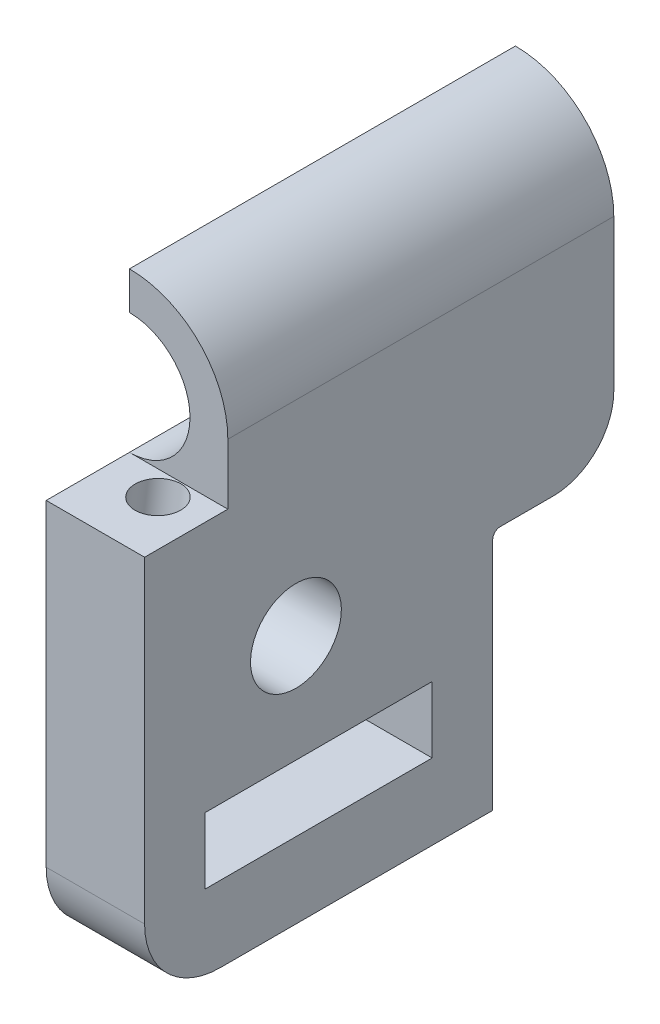
SolidWorks part; units mm, degrees
ref_plane "Front Plane" through (0, 0, 0) normal (0, 0, 1) x (1, 0, 0)
ref_plane "Top Plane" through (0, 0, 0) normal (0, 1, 0) x (1, 0, 0)
ref_plane "Right Plane" through (0, 0, 0) normal (1, 0, 0) x (0, 0, -1)
sketch "Sketch1" plane through (0, 0, 0) normal (0, 0, 1) x (1, 0, 0)
  line L0 (-3.75, 29) -> (-3.75, 22.5)
  line L2 (-3.75, 22.5) -> (-3.75, -22.5)
  line L3 (-3.75, -22.5) -> (2.75, -22.5)
  line L4 (2.75, 22.5) -> (2.75, -22.5)
  arc A0 (2.75, 22.5) -> (-3.75, 29) centre (-3.75, 22.5) ccw
  point P0 (0, 0)
  dimension "D1" = 6.5
  dimension "D2" = 45
extrude "Boss-Extrude1" add sketch "Sketch1" along normal blind 31
sketch "Sketch2" plane through (-3.75, 0, 0) normal (-1, 0, 0) x (0, 0, 1)
  line L5 (31, 29) -> (25.5, 29)
  line L6 (31, 29) -> (31, 18.5)
  line L7 (31, 18.5) -> (25.5, 18.5)
  line L8 (25.5, 29) -> (25.5, 18.5)
  dimension "D3" = 5.5
  dimension "D4" = 10.5
extrude "Cut-Extrude1" cut sketch "Sketch2" against normal through all
sketch "Sketch3" plane through (-3.75, 0, 0) normal (-1, 0, 0) x (0, 0, 1)
  line L0 (25.5, 29) -> (0, 29) construction
  line L1 (31, 18.5) -> (31, -22.5) construction
  line L3 (31, -22.5) -> (0, -22.5) construction
  circle A0 centre (21, 9) radius 3
  circle A1 centre (21, -12.5) radius 3
  dimension "D1" = 6
  dimension "D2" = 20
  dimension "D3" = 10
  dimension "D5" = 10
extrude "Cut-Extrude2" cut sketch "Sketch3" against normal through all
sketch "Sketch6" plane through (-3.75, 0, 0) normal (-1, 0, 0) x (0, 0, 1)
  line L1 (0, 8.5) -> (8, 8.5)
  line L2 (0, 8.5) -> (0, -4.5)
  line L3 (0, -4.5) -> (8, -4.5)
  line L4 (8, 8.5) -> (8, -4.5)
  line L6 (0, 29) -> (0, -22.5) construction
  line L7 (31, -22.5) -> (0, -22.5) construction
  dimension "D1" = 8
  dimension "D2" = 13
  dimension "D3" = 18
extrude "Cut-Extrude5" cut sketch "Sketch6" against normal up to next
fillet "Fillet1" radius 0.5 2 edges at (-0.5, -4.5, 8) (-0.5, 8.5, 8)
fillet "Fillet2" radius 4 2 edges at (-0.5, -4.5, 0) (-0.5, 8.5, 0)
sketch "Sketch8" plane through (0, 0, 25.5) normal (0, 0, 1) x (1, 0, 0)
  line L0 (-3.75, 29) -> (-3.75, 18.5) construction
  line L1 (2.75, 18.5) -> (-3.75, 18.5) construction
  line L2 (-3.75, 26.5) -> (-3.75, 18.5)
  arc A0 (-3.75, 18.5) -> (-3.75, 26.5) centre (-3.75, 22.5) ccw
  dimension "D1" = 4
  dimension "D2" = 4
extrude "Cut-Extrude7" cut sketch "Sketch8" against normal up to next
ref_plane "Plane2" through (0, 14.6273, -2.0557) normal (0, 0.9903, -0.1392) x (-1, 0, 0)
sketch "Sketch9" plane through (0, 14.6273, -2.0557) normal (0, 0.9903, -0.1392) x (-1, 0, 0)
  line L0 (-2.75, 27.8265) -> (-2.75, 33.273) construction
  line L1 (-2.75, 27.8265) -> (3.75, 27.8265) construction
  circle A0 centre (0.25, 29.4265) radius 1.5
  dimension "D1" = 3
  dimension "D2" = 3
  dimension "D3" = 1.6
extrude "Cut-Extrude8" cut sketch "Sketch9" against normal blind 17 contours A0
sketch "Sketch10" plane through (-3.75, 0, 0) normal (-1, 0, 0) x (0, 0, 1)
  line L0 (8, -7.4866) -> (35.2024, -7.4866)
  line L1 (21, 9) -> (32.765, 9) construction
  line L2 (8, -7.4866) -> (8, -2.8841)
  line L3 (8, -4) -> (8, 8) construction
  line L4 (-1.765, -2.8841) -> (8, -2.8841)
  line L5 (-1.765, -2.8841) -> (-1.765, -24.0083)
  line L6 (-1.765, -24.0083) -> (35.2024, -24.0083)
  line L7 (35.2024, -24.0083) -> (35.2024, -7.4866)
  dimension "D1" = 16.4866
extrude "Cut-Extrude9" cut sketch "Sketch10" against normal blind 10
fillet "Fillet3" radius 5 1 edges at (-0.5, -7.4866, 31)
sketch "Sketch11" plane through (-3.75, 0, 0) normal (-1, 0, 0) x (0, 0, 1)
  line L0 (26, -7.4866) -> (8, -7.4866) construction
  line L1 (12, 1.888) -> (27, 1.888)
  line L2 (12, 1.888) -> (12, -2.4866)
  line L3 (12, -2.4866) -> (27, -2.4866)
  line L4 (27, 1.888) -> (27, -2.4866)
  line L5 (31, 18.5) -> (31, -2.4866) construction
  line L6 (8, -7.4866) -> (8, 8) construction
  dimension "D1" = 5
  dimension "D2" = 4
  dimension "D3" = 4
extrude "Cut-Extrude10" cut sketch "Sketch11" against normal through all
